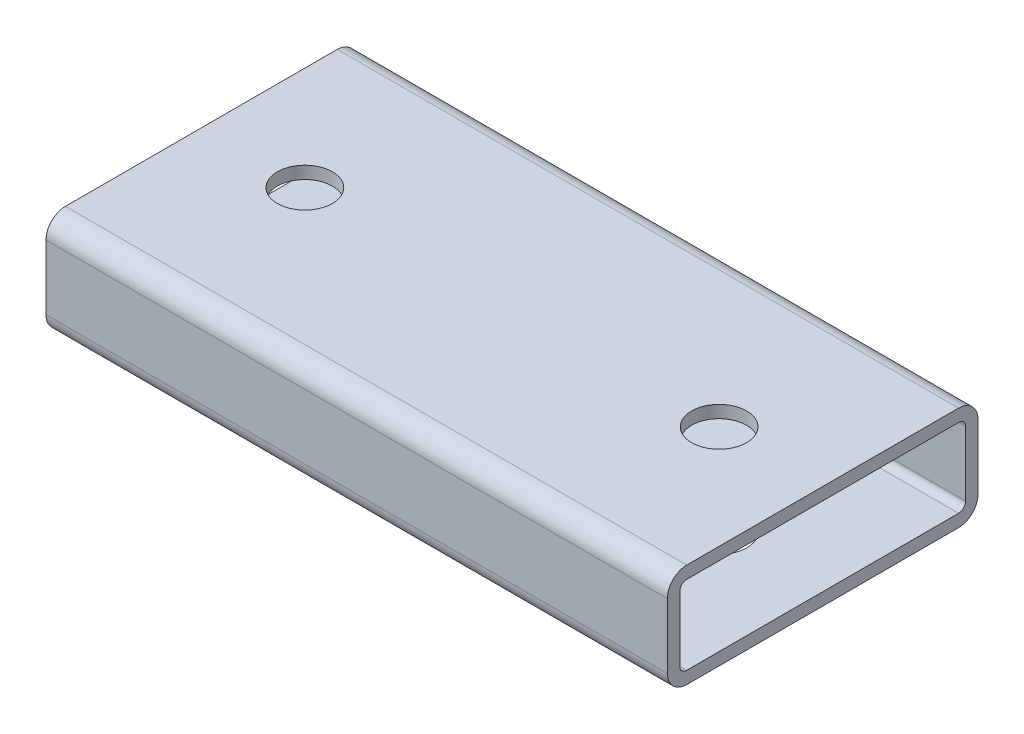
SolidWorks part; units mm, degrees
material "Plain Carbon Steel"
ref_plane "Front Plane" through (0, 0, 0) normal (0, 0, 1) x (1, 0, 0)
ref_plane "Top Plane" through (0, 0, 0) normal (0, 1, 0) x (1, 0, 0)
ref_plane "Right Plane" through (0, 0, 0) normal (1, 0, 0) x (0, 0, -1)
sketch "Sketch1" plane through (0, 0, 0) normal (0, 1, 0) x (1, 0, 0)
  line L0 (76.2, 0) -> (-76.2, 0)
  point P4 (0, 0)
  dimension "D1" = 152.4
other "Rectangular tube 3 X 2 X 0.25(1)"
ref_plane "Plane1" through (76.2, 0, 0) normal (-1, 0, 0) x (0, 0, 1)
sketch "Sketch16" plane through (76.2, 0, 0) normal (-1, 0, 0) x (0, 0, 1)
  line L0 (-33.3375, -9.652) -> (33.3375, -9.652)
  line L1 (-35.052, -7.9375) -> (-35.052, 7.9375)
  line L2 (33.3375, 9.652) -> (-33.3375, 9.652)
  line L3 (35.052, 7.9375) -> (35.052, -7.9375)
  line L4 (-33.3375, -12.7) -> (33.3375, -12.7)
  line L5 (-38.1, -7.9375) -> (-38.1, 7.9375)
  line L6 (33.3375, 12.7) -> (-33.3375, 12.7)
  line L7 (38.1, 7.9375) -> (38.1, -7.9375)
  line L8 (0, 0) -> (38.1, 0) construction
  line L9 (0, 0) -> (0, 12.7) construction
  arc A0 (38.1, 7.9375) -> (33.3375, 12.7) centre (33.3375, 7.9375) ccw
  arc A1 (33.3375, -12.7) -> (38.1, -7.9375) centre (33.3375, -7.9375) ccw
  arc A2 (-38.1, -7.9375) -> (-33.3375, -12.7) centre (-33.3375, -7.9375) ccw
  arc A3 (-33.3375, 12.7) -> (-38.1, 7.9375) centre (-33.3375, 7.9375) ccw
  arc A4 (-33.3375, 9.652) -> (-35.052, 7.9375) centre (-33.3375, 7.9375) ccw
  arc A5 (35.052, 7.9375) -> (33.3375, 9.652) centre (33.3375, 7.9375) ccw
  arc A6 (33.3375, -9.652) -> (35.052, -7.9375) centre (33.3375, -7.9375) ccw
  arc A7 (-35.052, -7.9375) -> (-33.3375, -9.652) centre (-33.3375, -7.9375) ccw
  point P3 (0, -12.7)
  point P4 (-38.1, 0)
  point P5 (0, 0)
  point P6 (38.1, -12.7)
  point P7 (-38.1, -12.7)
  point P8 (-38.1, 12.7)
  point P33 (0, 0)
  point P35 (38.1, 12.7)
  point P36 (38.1, 0)
  point P37 (0, 12.7)
  dimension "D1" = 4.7625
  dimension "Thickness" = 3.048
  dimension "V_leg" = 25.4
  dimension "H_leg" = 76.2
sketch "Sketch12" plane through (0, 12.7, 0) normal (0, 1, 0) x (1, 0, 0)
  line L0 (50.8, 0) -> (-50.8, 0)
  line L1 (76.2, 0) -> (-76.2, 0) construction
  point P5 (0, 0)
  dimension "D1" = 101.6
hole_wizard "1/2 Clearance Hole1" positions "Sketch13" profile "Sketch14" hole size "1/2" standard "ANSI Inch" end condition through all
sketch "Sketch13" plane through (0, 12.7, 0) normal (0, 1, 0) x (1, 0, 0)
  point P0 (-50.8, 0)
  point P3 (50.8, 0)
sketch "Sketch14" plane through (-50.8, 12.7, 0) normal (1, 0, 0) x (0, 0, 1)
  line L0 (0, 0) -> (0, 25.4)
  line L1 (0, 25.4) -> (6.7462, 25.4)
  line L2 (6.7462, 25.4) -> (6.7462, 0)
  line L5 (6.7462, 0) -> (0, 0)
  line L11 (0, -6.35) -> (0, 107.95) construction
  dimension "Thru Hole Dia." = 13.4925
  dimension "Thru Hole Depth" = 25.4
